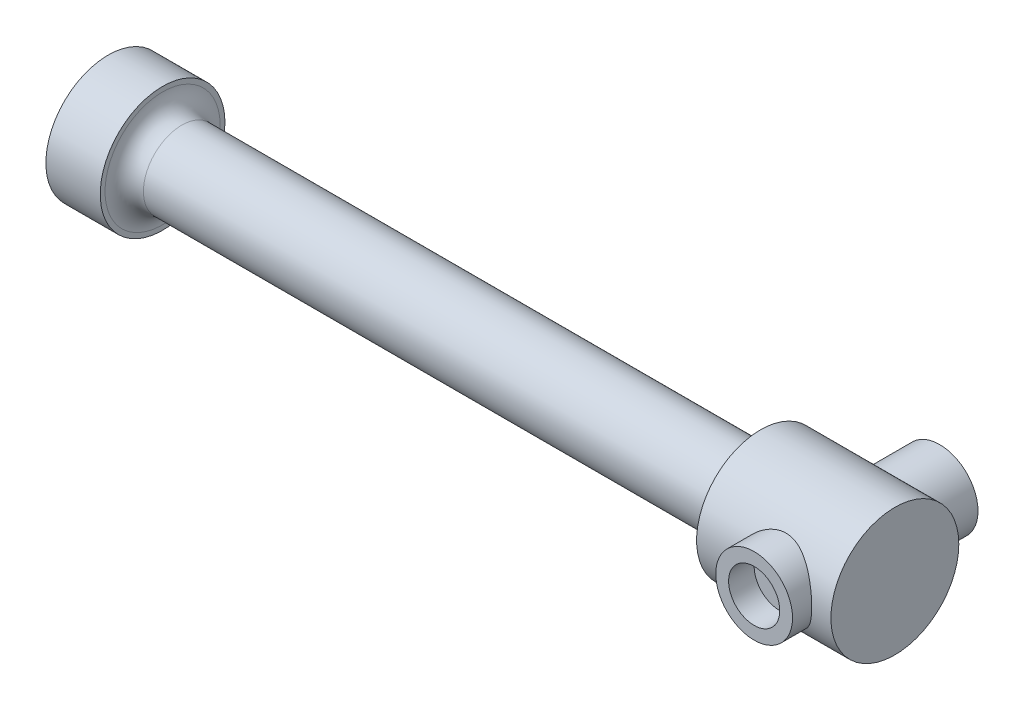
SolidWorks part; units mm, degrees
ref_plane "Front Plane" through (0, 0, 0) normal (0, 0, 1) x (1, 0, 0)
ref_plane "Top Plane" through (0, 0, 0) normal (0, 1, 0) x (1, 0, 0)
ref_plane "Right Plane" through (0, 0, 0) normal (1, 0, 0) x (0, 0, -1)
sketch "Sketch2" plane through (0, 0, 0) normal (1, 0, 0) x (0, 0, -1)
  circle A0 centre (0, 0) radius 9.75
  dimension "D1" = 19.5
extrude "Boss-Extrude1" add sketch "Sketch2" along normal blind 8.5
sketch "Sketch3" plane through (8.5, 0, 0) normal (1, 0, 0) x (0, 0, -1)
  circle A0 centre (0, 0) radius 6
  dimension "D1" = 12
extrude "Boss-Extrude2" add sketch "Sketch3" along normal blind 93.5
fillet "Fillet1" radius 3 1 edges at (8.5, 0, -6)
sketch "Sketch4" plane through (102, 0, 0) normal (1, 0, 0) x (0, 0, -1)
  circle A0 centre (0, 0) radius 10
  dimension "D1" = 20
extrude "Boss-Extrude3" add sketch "Sketch4" along normal blind 21
fillet "Fillet2" radius 2 1 edges at (102, 0, -6)
sketch "Sketch5" plane through (0, 0, 0) normal (0, 0, 1) x (1, 0, 0)
  line L0 (123, -10) -> (123, 10) construction
  line L1 (0, 0) -> (114, 0) construction
  circle A0 centre (114, 0) radius 6
  dimension "D1" = 12
  dimension "D2" = 9
extrude "Boss-Extrude4" add sketch "Sketch5" along normal blind 13 and the other way blind 16
sketch "Sketch6" plane through (0, 0, 13) normal (0, 0, 1) x (1, 0, 0)
  circle A0 centre (114, 0) radius 4
  dimension "D1" = 8
extrude "Cut-Extrude1" cut sketch "Sketch6" against normal blind 4
sketch "Sketch7" plane through (0, 0, 9) normal (0, 0, 1) x (1, 0, 0)
  circle A0 centre (114, 0) radius 1.5
  dimension "D1" = 3
extrude "Cut-Extrude2" cut sketch "Sketch7" against normal up to next
sketch "Sketch8" plane through (0, 0, -16) normal (0, 0, -1) x (-1, 0, 0)
  circle A0 centre (-114, 0) radius 4
  dimension "D1" = 8
extrude "Cut-Extrude3" cut sketch "Sketch8" against normal blind 4
